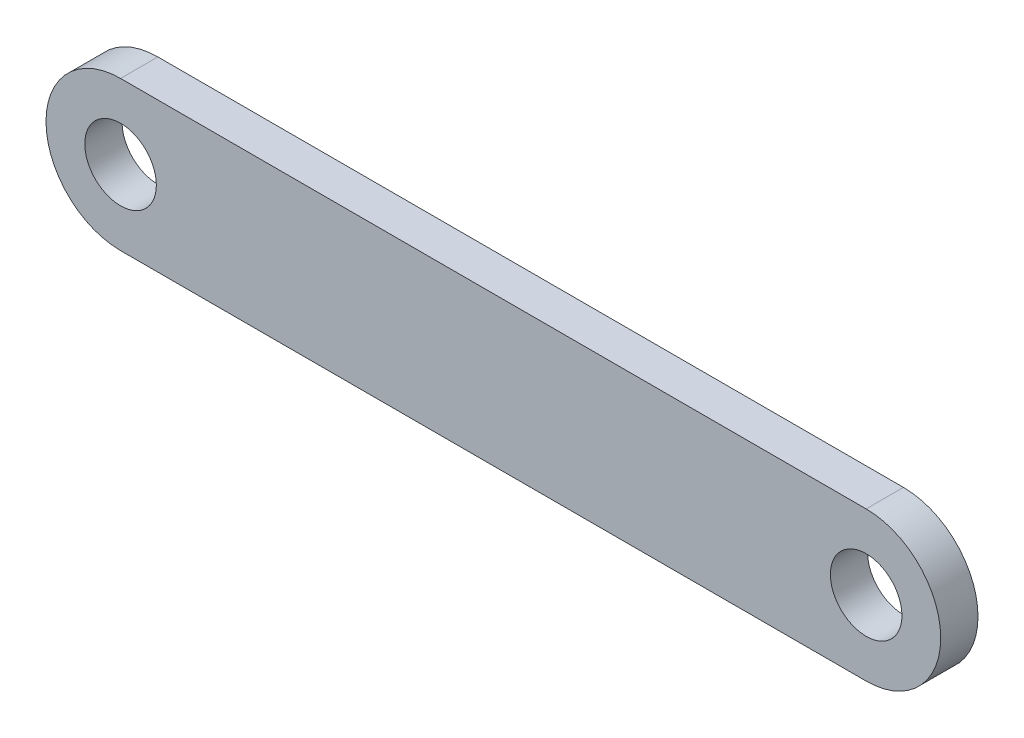
SolidWorks part; units mm, degrees
ref_plane "Front" through (0, 0, 0) normal (0, 0, 1) x (1, 0, 0)
ref_plane "Top" through (0, 0, 0) normal (0, 1, 0) x (1, 0, 0)
ref_plane "Right" through (0, 0, 0) normal (1, 0, 0) x (0, 0, -1)
sketch "Sketch1" plane through (0, 0, 0) normal (0, 0, 1) x (1, 0, 0)
  line L1 (-31.75, -6.35) -> (31.75, -6.35)
  line L2 (-31.75, -6.35) -> (-31.75, 6.35) construction
  line L3 (-31.75, 6.35) -> (31.75, 6.35)
  line L4 (31.75, -6.35) -> (31.75, 6.35) construction
  line L5 (-31.75, -6.35) -> (31.75, 6.35) construction
  line L6 (-31.75, 6.35) -> (31.75, -6.35) construction
  arc A0 (31.75, -6.35) -> (31.75, 6.35) centre (31.75, 0) ccw
  arc A1 (-31.75, 6.35) -> (-31.75, -6.35) centre (-31.75, 0) ccw
  circle A2 centre (31.75, 0) radius 3.048
  circle A3 centre (-31.75, 0) radius 3.048
  point P0 (0, 0)
  dimension "D3" = 6.096
  dimension "D4" = 6.096
  dimension "D1" = 12.7
  dimension "D2" = 63.5
extrude "Boss-Extrude1" add sketch "Sketch1" along normal blind 3.175
